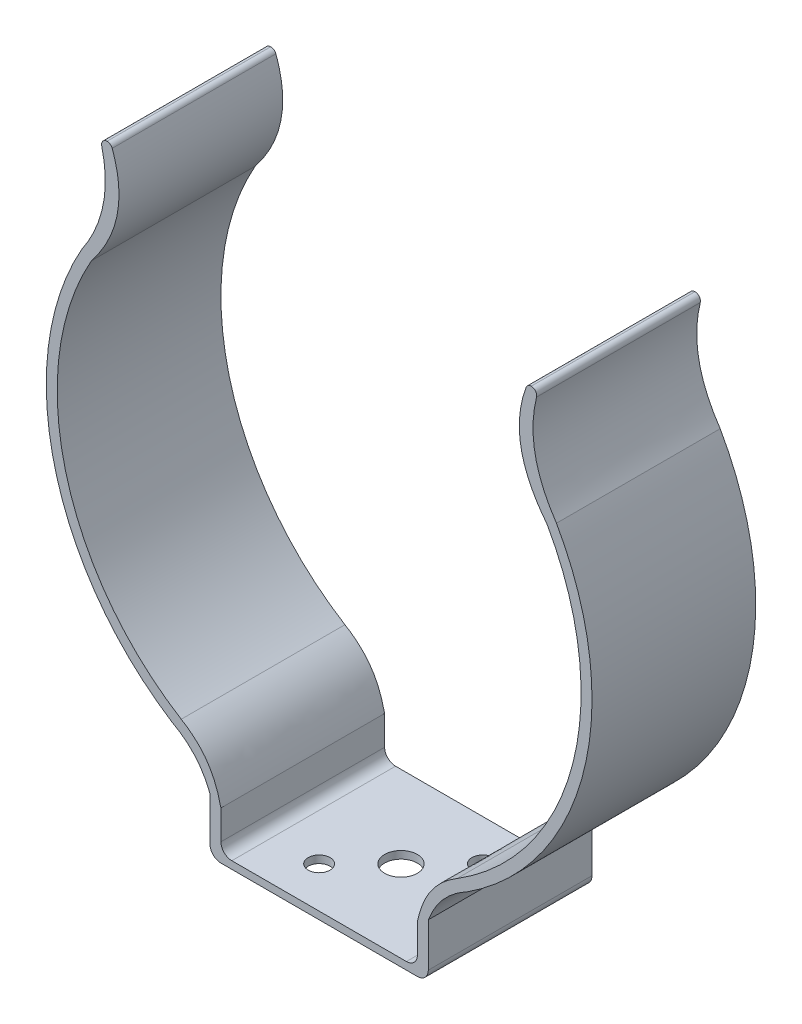
SolidWorks part; units mm, degrees
ref_plane "Front" through (0, 0, 0) normal (0, 0, 1) x (1, 0, 0)
ref_plane "Top" through (0, 0, 0) normal (0, 1, 0) x (1, 0, 0)
ref_plane "Right" through (0, 0, 0) normal (1, 0, 0) x (0, 0, -1)
sketch "Sketch1" plane through (0, 0, 0) normal (0, 0, 1) x (1, 0, 0)
  line L0 (-51.0305, 56.0232) -> (-48.4905, 56.0232)
  line L1 (0, 0) -> (0, 35.1132) construction
  line L2 (51.0305, 56.0232) -> (48.4905, 56.0232)
  line L5 (-25.4, -63.5) -> (-25.4, -76.2)
  line L6 (-25.4, -76.2) -> (25.4, -76.2)
  line L7 (25.4, -63.5) -> (25.4, -76.2)
  line L9 (-22.86, -65.0923) -> (-22.86, -74.4492)
  line L10 (-22.86, -74.4492) -> (22.86, -74.4492)
  line L11 (22.86, -65.0923) -> (22.86, -74.4492)
  arc A0 (-55.2244, 31.3451) -> (-34.3107, -53.4325) centre (0, 0) ccw
  arc A1 (-53.0154, 30.0913) -> (-32.0965, -51.826) centre (0, 0) ccw
  arc A2 (34.3107, -53.4325) -> (55.2244, 31.3451) centre (0, 0) ccw
  arc A3 (32.0965, -51.826) -> (53.0154, 30.0913) centre (0, 0) ccw
  spline S0 degree 2 poles (-55.2244, 31.3451) (-47.1441, 43.197) (-51.0305, 56.0232) knots 0 0 0 1 1 1
  spline S1 degree 2 poles (-48.4905, 56.0232) (-43.0693, 42.6114) (-53.0154, 30.0913) knots 0 0 0 1 1 1
  spline S2 degree 2 poles (48.4905, 56.0232) (43.0693, 42.6114) (53.0154, 30.0913) knots 0 0 0 1 1 1
  spline S3 degree 2 poles (55.2244, 31.3451) (47.1441, 43.197) (51.0305, 56.0232) knots 0 0 0 1 1 1
  spline S4 degree 2 poles (-34.3107, -53.4325) (-27.9325, -56.814) (-25.4, -63.5) knots 0 0 0 1 1 1
  spline S5 degree 3 poles (-32.0965, -51.826) (-26.6666, -55.0807) (-24.1541, -59.2741) (-22.86, -65.0923) knots 0 0 0 0 1 1 1 1
  spline S6 degree 3 poles (32.0965, -51.826) (26.6666, -55.0807) (24.1541, -59.2741) (22.86, -65.0923) knots 0 0 0 0 1 1 1 1
  spline S7 degree 2 poles (34.3107, -53.4325) (27.9325, -56.814) (25.4, -63.5) knots 0 0 0 1 1 1
  dimension "D1" = 127
  dimension "D4" = 121.92
  dimension "D5" = 12.7
  dimension "D2" = 2.54
  dimension "D3" = 2.54
  dimension "D6" = 50.8
  dimension "D8" = 2.54
extrude "Boss-Extrude1" add sketch "Sketch1" along normal blind 38.1
sketch "Sketch2" plane through (0, -74.4492, 0) normal (0, 1, 0) x (1, 0, 0)
  line L1 (-9.525, -9.525) -> (9.525, -9.525) construction
  line L2 (-9.525, -9.525) -> (-9.525, -28.575) construction
  line L3 (-9.525, -28.575) -> (9.525, -28.575) construction
  line L4 (9.525, -9.525) -> (9.525, -28.575) construction
  circle A0 centre (0, -19.05) radius 3.81
  circle A2 centre (9.525, -9.525) radius 2.54
  circle A3 centre (-9.525, -28.575) radius 2.54
  point P4 (0, -9.525)
  point P10 (9.525, -19.05)
  point P11 (0, -28.575)
  dimension "D4" = 7.62
  dimension "D5" = 5.08
  dimension "D1" = 19.05
  dimension "D2" = 19.05
  dimension "D3" = 9.525
extrude "Cut-Extrude1" cut sketch "Sketch2" against normal blind 2.54
fillet "Fillet1" radius 1.27 4 edges at (51.0305, 56.0232, 19.05) (48.4905, 56.0232, 19.05) (-48.4905, 56.0232, 19.05) (-51.0305, 56.0232, 19.05)
fillet "Fillet2" radius 2.54 4 edges at (25.4, -76.2, 19.05) (-25.4, -76.2, 19.05) (22.86, -74.4492, 19.05) (-22.86, -74.4492, 19.05)
scale "Scale1" scale about origin uniform scaling yes scale factor 1.1
